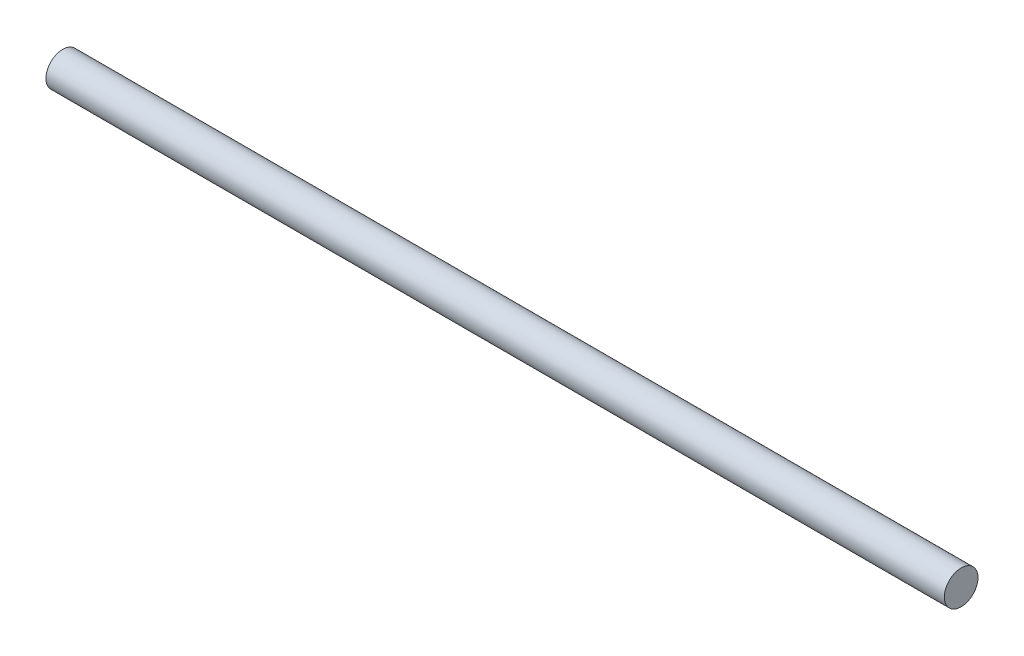
SolidWorks part; units mm, degrees
ref_plane "Front Plane" through (0, 0, 0) normal (0, 0, 1) x (1, 0, 0)
ref_plane "Top Plane" through (0, 0, 0) normal (0, 1, 0) x (1, 0, 0)
ref_plane "Right Plane" through (0, 0, 0) normal (1, 0, 0) x (0, 0, -1)
sketch "Sketch6" plane through (0, 0, 0) normal (0, 0, 1) x (1, 0, 0)
  line L1 (0, 0) -> (10.16, 0)
  dimension "D1" = 10.16
sweep "Sweep2" add path "Sketch6" circular profile diameter 0.381 parameters "D3"=0.381
